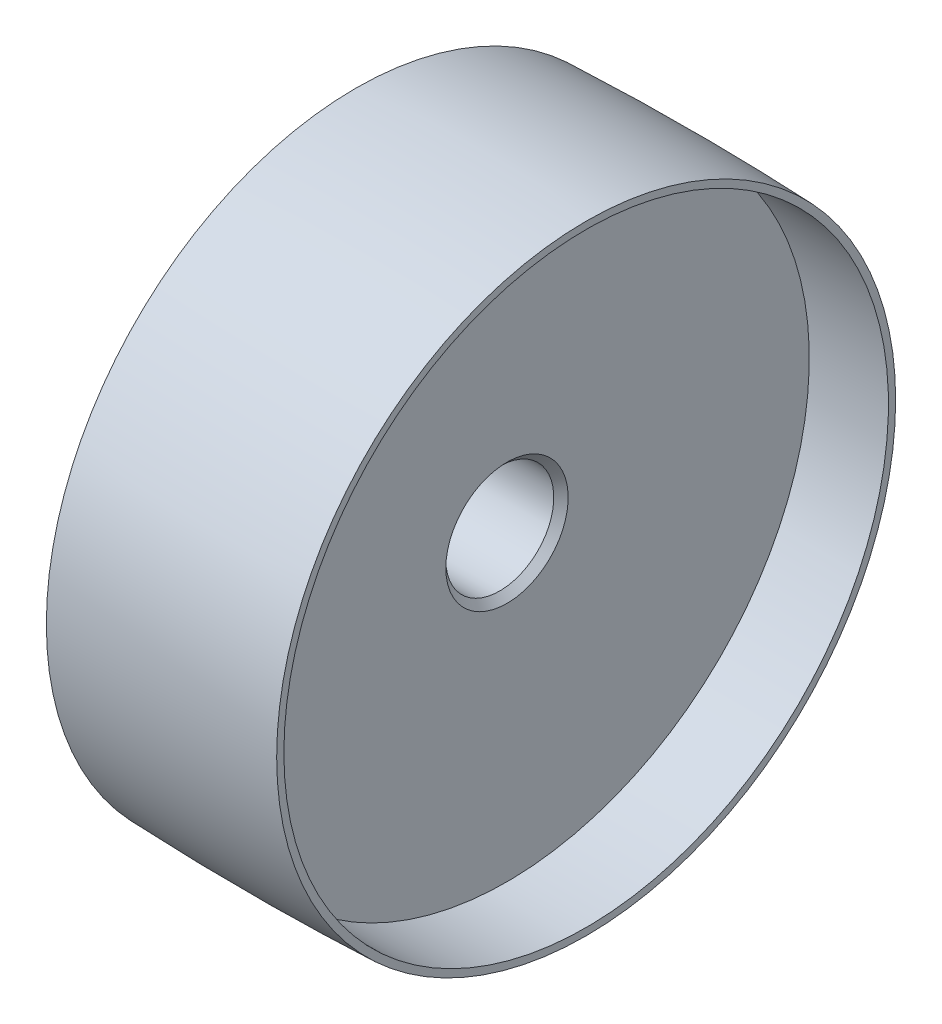
SolidWorks part; units mm, degrees
material "Сталь 40Х ГОСТ 4543-71"
ref_plane "Спереди (Плоскость XY)" through (0, 0, 0) normal (0, 0, 1) x (1, 0, 0)
ref_plane "Сверху (Плоскость XZ)" through (0, 0, 0) normal (0, 1, 0) x (1, 0, 0)
ref_plane "Справа (Плоскость ZY)" through (0, 0, 0) normal (1, 0, 0) x (0, 0, -1)
other "Configuration Table"
sketch "Эскиз1" plane through (0, 0, 0) normal (0, 0, 1) x (1, 0, 0)
  line L0 (0, 0) -> (87.0994, 0) construction
  line L1 (0, 7.5) -> (0, 15)
  line L2 (0, 15) -> (11, 15)
  line L3 (11, 15) -> (11, 42)
  line L4 (11, 42) -> (0, 42)
  line L5 (0, 42) -> (0, 43)
  line L6 (0, 7.5) -> (21, 7.5)
  line L7 (16, 47.7951) -> (16, 7.5) construction
  line L10 (21, 7.5) -> (21, 42)
  line L11 (21, 42) -> (32, 42)
  line L12 (32, 42) -> (32, 43)
  arc A2 (0, 43) -> (32, 43) centre (16, -383.5167) cw
  point P19 (16, 43.3)
  dimension "D1" = 0.3
  dimension "D2" = 15
  dimension "D3" = 30
  dimension "D4" = 1
  dimension "D5" = 84
  dimension "D6" = 16
  dimension "D7" = 10
revolve "Повернуть1" add sketch "Эскиз1" angle 360 about L0
chamfer "Фаска2" distance 1 angle 45 3 edges at (0, 0, 7.5) (21, 0, 7.5) (0, 0, 15)
